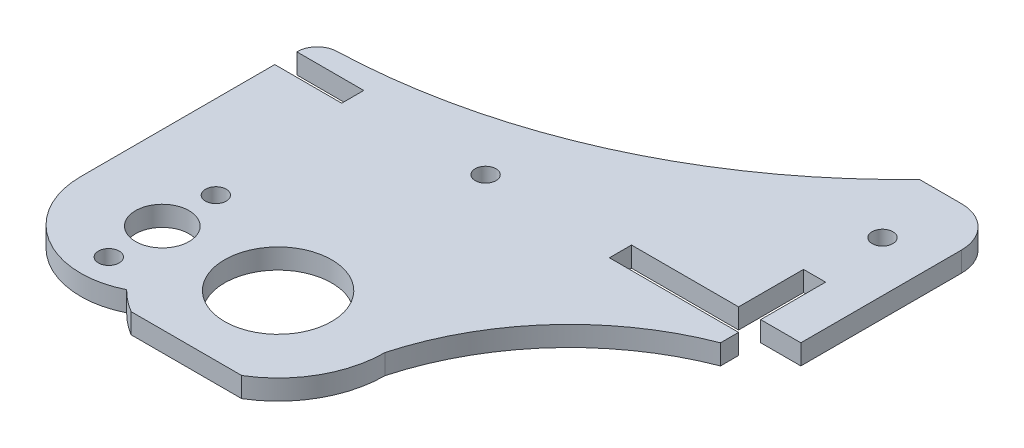
SolidWorks part; units mm, degrees
ref_plane "Alzado" through (0, 0, 0) normal (0, 0, 1) x (1, 0, 0)
ref_plane "Planta" through (0, 0, 0) normal (0, 1, 0) x (1, 0, 0)
ref_plane "Vista lateral" through (0, 0, 0) normal (1, 0, 0) x (0, 0, -1)
sketch "Croquis1" plane through (0, 0, 0) normal (0, 1, 0) x (1, 0, 0)
  line L0 (0, 38.7) -> (69.3, 38.7) construction
  line L1 (0, 0) -> (69.3, 0) construction
  line L2 (0, 0) -> (0, 38.7)
  line L3 (0, 72) -> (69.3, 72)
  line L4 (69.3, 0) -> (69.3, 38.7)
  line L5 (69.3, 51.7) -> (69.3, 72) construction
  line L8 (69.3, 51.7) -> (66, 51.7)
  line L9 (66, 42) -> (66, 51.7)
  line L11 (69.3, 38.7) -> (50, 38.7)
  line L13 (66, 42) -> (50, 42)
  line L14 (50, 38.7) -> (50, 42)
  line L15 (0, 38.7) -> (10, 38.7)
  line L17 (0, 42) -> (10, 42)
  line L18 (10, 38.7) -> (10, 42)
  line L19 (0, 42) -> (0, 72)
  line L20 (69.3, 72) -> (75.3, 72)
  line L21 (69.3, 72) -> (69.3, 51.7) construction
  line L23 (75.3, 72) -> (75.3, 52)
  line L25 (69.3, 51.7) -> (69.3, 42)
  line L26 (69.3, 42) -> (75.3, 42)
  line L27 (75.3, 52) -> (75.3, 42)
  line L28 (0, 0) -> (69.3, 0) construction
  line L29 (0, 0) -> (0, -4)
  line L30 (0, -4) -> (69.3, -4)
  line L31 (69.3, 0) -> (69.3, -4)
  circle A0 centre (30, 40.2) radius 1.55
  circle A1 centre (67.8, 61.7) radius 1.55
  circle A2 centre (12.5, 9.4) radius 4
  dimension "D9" = 3.1
  dimension "D13" = 6
  dimension "D14" = 3.1
  dimension "D18" = 8
  dimension "D2" = 72
  dimension "D3" = 3.3
  dimension "D4" = 13
  dimension "D5" = 16
  dimension "D6" = 3.3
  dimension "D7" = 3.3
  dimension "D8" = 10
  dimension "D10" = 30
  dimension "D11" = 20
  dimension "D12" = 1.5
  dimension "D15" = 1.5
  dimension "D16" = 10
  dimension "D17" = 40
  dimension "D19" = 29.3
  dimension "D20" = 12.5
  dimension "D21" = 30
  dimension "D22" = 4
extrude "Saliente-Extruir10" add sketch "Croquis1" along normal blind 3
sketch "Croquis2" plane through (0, 3, 0) normal (0, 1, 0) x (1, 0, 0)
  line L0 (12.5, 9.4) -> (12.5, 29.073) construction
  circle A0 centre (29.5, 9.7) radius 8
  circle A1 centre (12.5, 17.4) radius 1.55
  circle A2 centre (12.5, 1.4) radius 1.55
  circle A3 centre (12.5, 9.4) radius 4 construction
  circle A4 centre (12.5, 9.4) radius 4 construction
  dimension "D1" = 16
  dimension "D2" = 3.1
  dimension "D3" = 8
  dimension "D4" = 8
extrude "Cortar-Extruir1" cut sketch "Croquis2" against normal up to surface (3 mm away) up to face at (42.4875, 0, -40.3875)
sketch "Croquis3" plane through (0, 3, 0) normal (0, 1, 0) x (1, 0, 0)
  line L1 (0, 72) -> (63, 72)
  line L2 (0, 72) -> (0, 45)
  line L7 (69.3, -4) -> (45.5, -4)
  line L8 (69.3, -4) -> (69.3, 36)
  line L10 (45.5, -4) -> (45.5, 9.7)
  line L11 (0, 9.7) -> (0, -4)
  line L12 (0, -4) -> (21.235, -4)
  line L13 (0, -4) -> (69.3, -4) construction
  line L14 (45.5, -4) -> (37.765, -4)
  line L15 (37.765, -4) -> (45.5, -4)
  circle A0 centre (29.5, 9.7) radius 8.8 construction
  arc A1 (63, 72) -> (0, 45) centre (0, 132) cw
  arc A2 (18.0662, -1.4923) -> (45.5, 9.7) centre (29.5, 9.7) ccw
  arc A3 (0, 9.7) -> (18.0662, -1.4923) centre (12.5, 9.7) ccw
  arc A4 (45.5, 9.7) -> (69.3, 36) centre (83.4996, -0.7686) cw
  circle M21 centre (29.5, 9.7) radius 8
  circle M22 centre (67.8, 61.7) radius 1.55
  line M23 (0, 38.7) -> (0, -4)
  line M24 (0, -4) -> (69.3, -4)
  line M25 (69.3, -4) -> (69.3, 38.7)
  line M26 (69.3, 38.7) -> (50, 38.7)
  line M27 (50, 38.7) -> (50, 42)
  line M28 (50, 42) -> (66, 42)
  line M29 (66, 42) -> (66, 51.7)
  line M30 (66, 51.7) -> (69.3, 51.7)
  line M31 (69.3, 51.7) -> (69.3, 42)
  line M32 (69.3, 42) -> (75.3, 42)
  line M33 (75.3, 42) -> (75.3, 72)
  line M34 (75.3, 72) -> (0, 72)
  line M35 (0, 72) -> (0, 42)
  line M36 (0, 42) -> (10, 42)
  line M37 (10, 42) -> (10, 38.7)
  line M38 (10, 38.7) -> (0, 38.7)
  circle M39 centre (30, 40.2) radius 1.55
  circle M40 centre (12.5, 9.4) radius 4
  dimension "D4" = 16
extrude "Cortar-Extruir2" cut sketch "Croquis3" against normal up to surface (3 mm away) flip side to cut contours A2 A4 A1 A3 M25 M26 M27 M28 M29 M30 M31 M32 M33 M34 M35 M36 M37 M38 M23 M24 M22 M39 M40 M21 up to face at (29.5, 0, -1.7)
fillet "Redondeo1" radius 6 1 edges at (75.3, 1.5, -72)
fillet "Redondeo2" radius 3 1 edges at (0, 1.5, -45)
